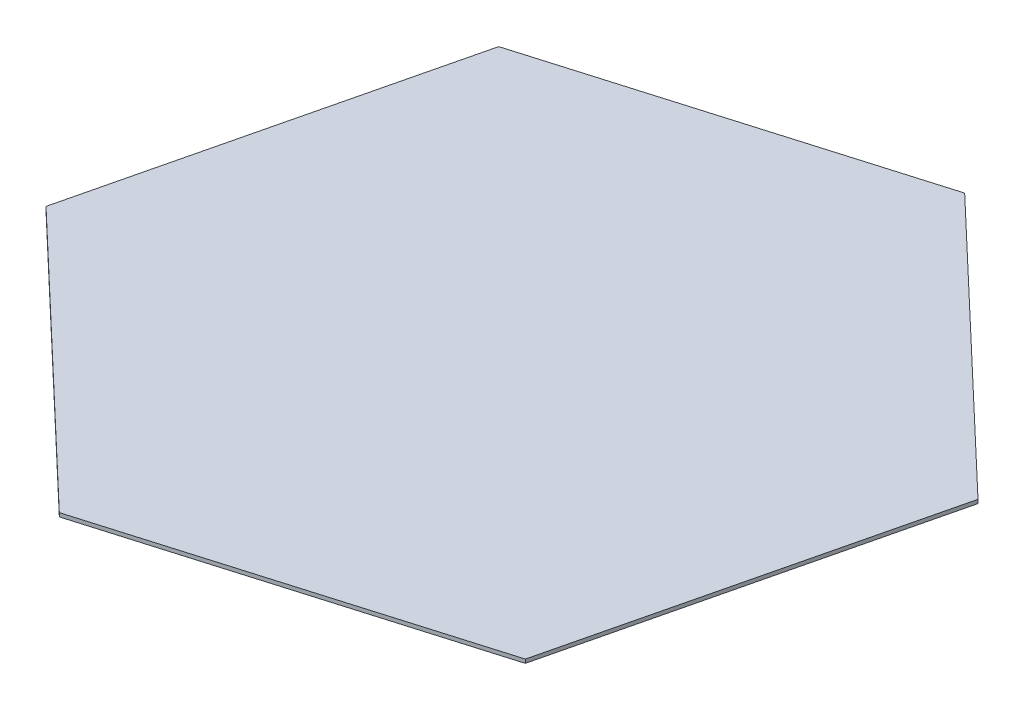
SolidWorks part; units mm, degrees
ref_plane "Front Plane" through (0, 0, 0) normal (0, 0, 1) x (1, 0, 0)
ref_plane "Top Plane" through (0, 0, 0) normal (0, 1, 0) x (1, 0, 0)
ref_plane "Right Plane" through (0, 0, 0) normal (1, 0, 0) x (0, 0, -1)
sketch "Sketch1" plane through (0, 0, 0) normal (0, 1, 0) x (1, 0, 0)
  line L0 (0, 0) -> (-191.8236, -56.6014) construction
  line L1 (-46.8936, -194.4248) -> (144.93, -137.8234)
  line L2 (144.93, -137.8234) -> (191.8236, 56.6014)
  line L3 (191.8236, 56.6014) -> (46.8936, 194.4248)
  line L4 (46.8936, 194.4248) -> (-144.93, 137.8234)
  line L5 (-144.93, 137.8234) -> (-191.8236, -56.6014)
  line L6 (-191.8236, -56.6014) -> (-46.8936, -194.4248)
  circle A0 centre (0, 0) radius 173.2051 construction
  dimension "D2" = 200
extrude "Boss-Extrude1" add sketch "Sketch1" along normal blind 2
